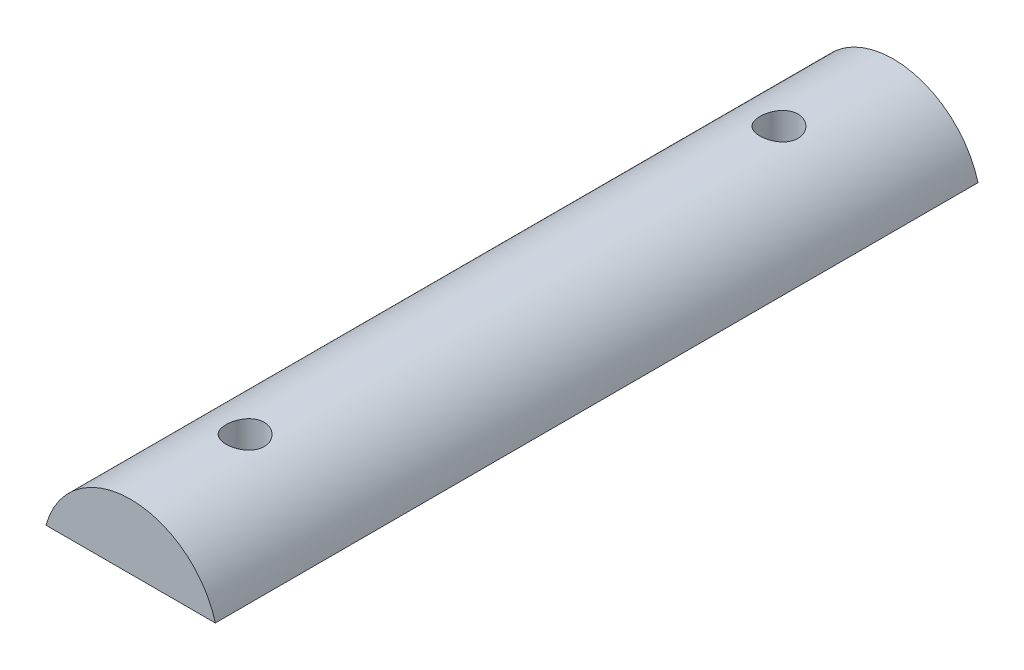
SolidWorks part; units mm, degrees
ref_plane "Alzado" through (0, 0, 0) normal (0, 0, 1) x (1, 0, 0)
ref_plane "Planta" through (0, 0, 0) normal (0, 1, 0) x (1, 0, 0)
ref_plane "Vista lateral" through (0, 0, 0) normal (1, 0, 0) x (0, 0, -1)
sketch "Croquis1" plane through (0, 0, 0) normal (0, 0, 1) x (1, 0, 0)
  line L0 (-47.5567, 5.9239) -> (-25.3531, 5.9239)
  arc A0 (-25.3531, 5.9239) -> (-47.5567, 5.9239) centre (-36.4549, 2.9239) ccw
  dimension "D1" = 23
  dimension "D2" = 3
extrude "Saliente-Extruir1" add sketch "Croquis1" along normal blind 100
sketch "Croquis2" plane through (0, 5.9239, 0) normal (0, -1, 0) x (1, 0, 0)
  line L0 (-47.5567, 100) -> (-25.3531, 100) construction
  line L1 (-36.4549, 80.3812) -> (-32.4549, 82.6906)
  line L2 (-32.4549, 82.6906) -> (-32.4549, 87.3094)
  line L3 (-32.4549, 87.3094) -> (-36.4549, 89.6188)
  line L4 (-36.4549, 89.6188) -> (-40.4549, 87.3094)
  line L5 (-40.4549, 87.3094) -> (-40.4549, 82.6906)
  line L6 (-40.4549, 82.6906) -> (-36.4549, 80.3812)
  line L7 (-36.4549, 10.3812) -> (-32.4549, 12.6906)
  line L8 (-32.4549, 12.6906) -> (-32.4549, 17.3094)
  line L9 (-32.4549, 17.3094) -> (-36.4549, 19.6188)
  line L10 (-36.4549, 19.6188) -> (-40.4549, 17.3094)
  line L11 (-40.4549, 17.3094) -> (-40.4549, 12.6906)
  line L12 (-40.4549, 12.6906) -> (-36.4549, 10.3812)
  line L13 (-47.5567, 0) -> (-25.3531, 0) construction
  circle A0 centre (-36.4549, 85) radius 4 construction
  circle A1 centre (-36.4549, 15) radius 4 construction
  dimension "D1" = 15
  dimension "D2" = 15
extrude "Cortar-Extruir1" cut sketch "Croquis2" against normal blind 4
sketch "Croquis3" plane through (0, 9.9239, 0) normal (0, -1, 0) x (1, 0, 0)
  circle A0 centre (-36.4549, 15) radius 2.5
  circle A1 centre (-36.4549, 85) radius 2.5
  dimension "D1" = 5
  dimension "D2" = 5
extrude "Cortar-Extruir2" cut sketch "Croquis3" against normal blind 14
